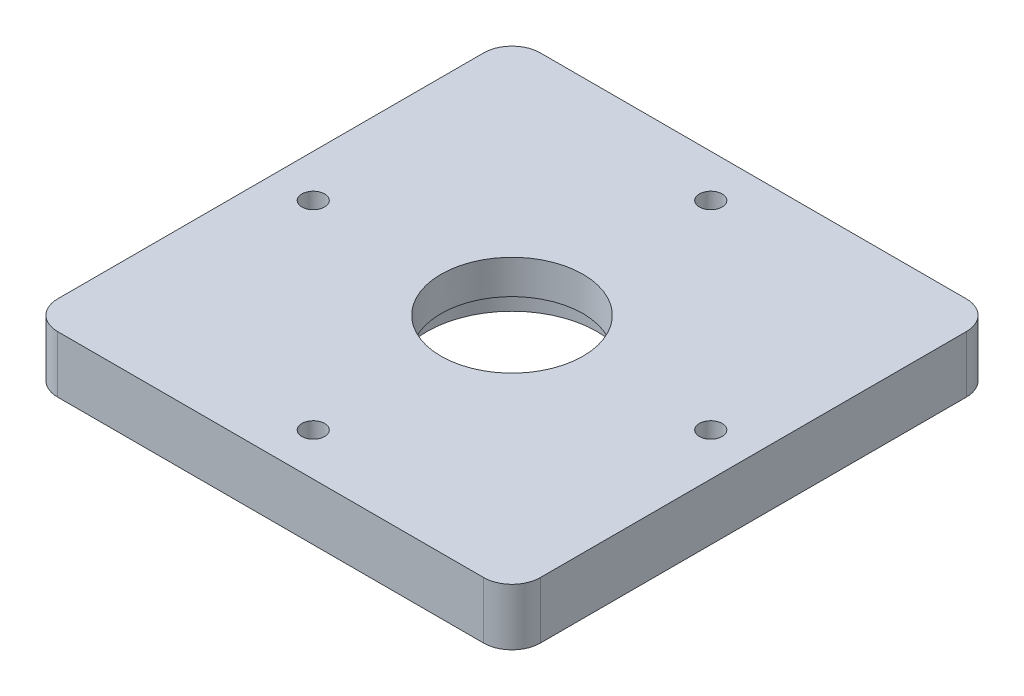
SolidWorks part; units mm, degrees
ref_plane "Front Plane" through (0, 0, 0) normal (0, 0, 1) x (1, 0, 0)
ref_plane "Top Plane" through (0, 0, 0) normal (0, 1, 0) x (1, 0, 0)
ref_plane "Right Plane" through (0, 0, 0) normal (1, 0, 0) x (0, 0, -1)
sketch "Sketch2" plane through (0, 0, 0) normal (0, 1, 0) x (1, 0, 0)
  line L0 (0, 0) -> (48777.2138, 0) construction
  line L1 (0, 0) -> (0, -48777.2138) construction
  line L3 (-85, 85) -> (85, 85)
  line L4 (-85, 85) -> (-85, -85)
  line L5 (-85, -85) -> (85, -85)
  line L6 (85, 85) -> (85, -85)
  line L7 (-85, 85) -> (85, -85) construction
  line L8 (-85, -85) -> (85, 85) construction
  point P5 (0, 0)
  dimension "D1" = 170
  dimension "D2" = 170
extrude "Boss-Extrude1" add sketch "Sketch2" along normal blind 20
fillet "Fillet1" radius 10 1 edges at (85, 10, 85)
fillet "Fillet2" radius 10 1 edges at (85, 10, -85)
fillet "Fillet3" radius 10 1 edges at (-85, 10, -85)
fillet "Fillet4" radius 10 1 edges at (-85, 10, 85)
sketch "Sketch11" plane through (0, 0, 0) normal (0, -1, 0) x (1, 0, 0)
  circle A0 centre (0, 0) radius 30
  dimension "D1" = 60
extrude "Cut-Extrude3" cut sketch "Sketch11" against normal blind 8
sketch "Sketch16" plane through (0, 8, 0) normal (0, -1, 0) x (1, 0, 0)
  circle A0 centre (0, 0) radius 25
  dimension "D1" = 50
extrude "Cut-Extrude4" cut sketch "Sketch16" against normal blind 96
hole_wizard "CBORE for M5 Hex Head Bolt4" positions "Sketch19" profile "Sketch20" counterbore size "M5" standard "ISO" end condition through all
sketch "Sketch19" plane through (0, 20, 0) normal (0, 1, 0) x (1, 0, 0)
  line L1 (0, 0) -> (0, -50000) construction
  line L2 (0, 0) -> (50000, 0) construction
  point P0 (0, 70)
  point P2 (0, -70)
  point P4 (70, 0)
  point P6 (-70, 0)
  dimension "D1" = 70
  dimension "D2" = 70
  dimension "D3" = 70
  dimension "D4" = 70
sketch "Sketch20" plane through (0, 20, -70) normal (1, 0, 0) x (0, 0, 1)
  line L0 (0, 0) -> (0, 20)
  line L1 (0, 20) -> (3, 20)
  line L3 (3, 20) -> (3, 6)
  line L4 (3, 6) -> (4, 6)
  line L5 (4, 6) -> (4, 0)
  line L7 (4, 0) -> (0, 0)
  line L11 (0, -6.35) -> (0, 107.95) construction
  dimension "Thru Hole Dia." = 6
  dimension "Thru Hole Depth" = 20
  dimension "C'Bore Dia." = 8
  dimension "C'Bore Depth" = 6
